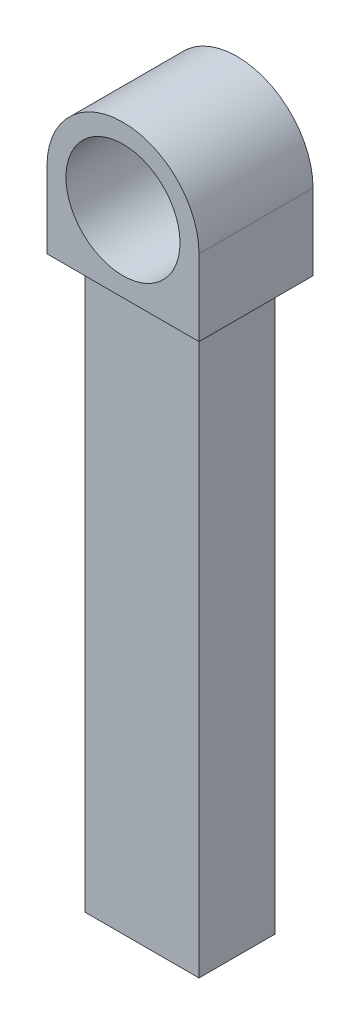
SolidWorks part; units mm, degrees
ref_plane "前视基准面" through (0, 0, 0) normal (0, 0, 1) x (1, 0, 0)
ref_plane "上视基准面" through (0, 0, 0) normal (0, 1, 0) x (1, 0, 0)
ref_plane "右视基准面" through (0, 0, 0) normal (1, 0, 0) x (0, 0, -1)
sketch "草图1" plane through (0, 0, 0) normal (0, 0, 1) x (1, 0, 0)
  line L0 (-2, 0) -> (-2, -2)
  line L1 (-2, -2) -> (2, -2)
  line L2 (2, -2) -> (2, 0)
  circle A0 centre (0, 0) radius 1.5
  circle A1 centre (0, 0) radius 2
  dimension "D1" = 3
  dimension "D2" = 4
extrude "凸台-拉伸1" add sketch "草图1" along normal blind 3 contours A1 L0 L1 | A1 A0 | A1 L1 L2
sketch "草图2" plane through (0, -2, 0) normal (0, -1, 0) x (1, 0, 0)
  line L0 (2, 3) -> (2, 0) construction
  line L1 (1.5, 2.5) -> (-1.5, 2.5)
  line L2 (1.5, 2.5) -> (1.5, 0.5)
  line L3 (1.5, 0.5) -> (-1.5, 0.5)
  line L4 (-1.5, 2.5) -> (-1.5, 0.5)
  line L6 (-2, 3) -> (2, 3) construction
  dimension "D1" = 2
  dimension "D2" = 3
  dimension "D3" = 0.5
  dimension "D4" = 0.5
extrude "凸台-拉伸2" add sketch "草图2" along normal blind 15
